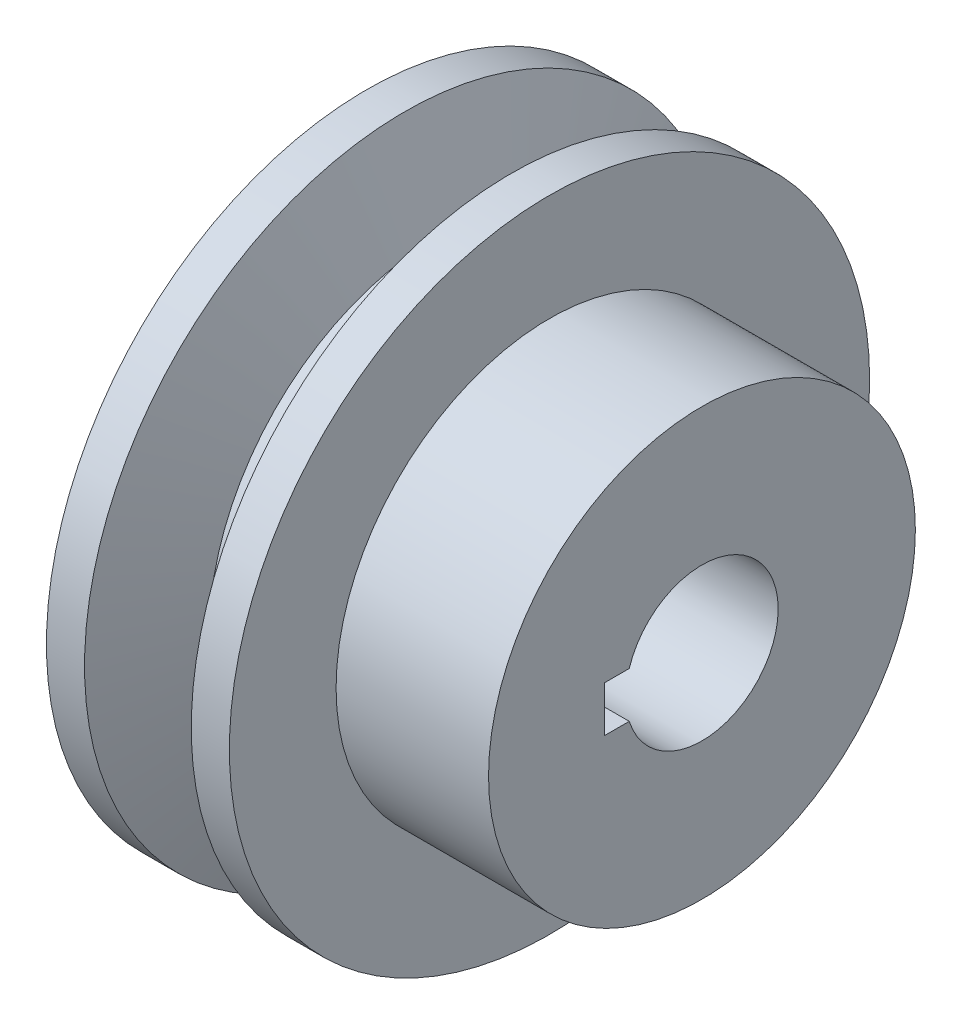
SolidWorks part; units mm, degrees
ref_plane "Front Plane" through (0, 0, 0) normal (0, 0, 1) x (1, 0, 0)
ref_plane "Top Plane" through (0, 0, 0) normal (0, 1, 0) x (1, 0, 0)
ref_plane "Right Plane" through (0, 0, 0) normal (1, 0, 0) x (0, 0, -1)
sketch "Sketch1" plane through (0, 0, 0) normal (0, 0, 1) x (1, 0, 0)
  line L0 (22, 0) -> (0, 0)
  line L1 (0, 0) -> (0, 21)
  line L2 (0, 21) -> (2.5, 21)
  line L3 (2.5, 21) -> (4.6838, 15)
  line L4 (4.6838, 15) -> (7.3162, 15)
  line L5 (7.3162, 15) -> (9.5, 21)
  line L6 (9.5, 21) -> (12, 21)
  line L7 (12, 21) -> (12, 14)
  line L8 (12, 14) -> (22, 14)
  line L9 (22, 14) -> (22, 0)
  line L10 (6, 15) -> (6, 21.4414) construction
  point P13 (4.519, 18.1424)
  point P14 (9.4114, 18.1577)
  point P15 (3.0625, 18.0754)
  point P16 (8.7666, 13.9141)
  point P17 (3.583, 18.2727)
  point P18 (4.9848, 14.5824)
  point P19 (7.7647, 16.2322)
  dimension "D1" = 22
  dimension "D2" = 12
  dimension "D3" = 40
  dimension "D4" = 7
  dimension "D5" = 21
  dimension "D6" = 14
  dimension "D7" = 15
revolve "Revolve1" add sketch "Sketch1" angle 360 about L0
sketch "Sketch2" plane through (0, 0, 0) normal (-1, 0, 0) x (0, 0, 1)
  line L0 (0, 0) -> (13.7799, 0) construction
  line L1 (6.4, 1.5) -> (6.4, -1.5)
  line L2 (6.4, -1.5) -> (4.7697, -1.5)
  line L3 (6.4, 1.5) -> (4.7697, 1.5)
  arc A0 (4.7697, 1.5) -> (4.7697, -1.5) centre (0, 0) ccw
  point P1 (6.3724, 1.5)
  dimension "D1" = 10
  dimension "D2" = 6.4
  dimension "D3" = 3
  dimension "D4" = 1.5
extrude "Cut-Extrude1" cut sketch "Sketch2" against normal through all
